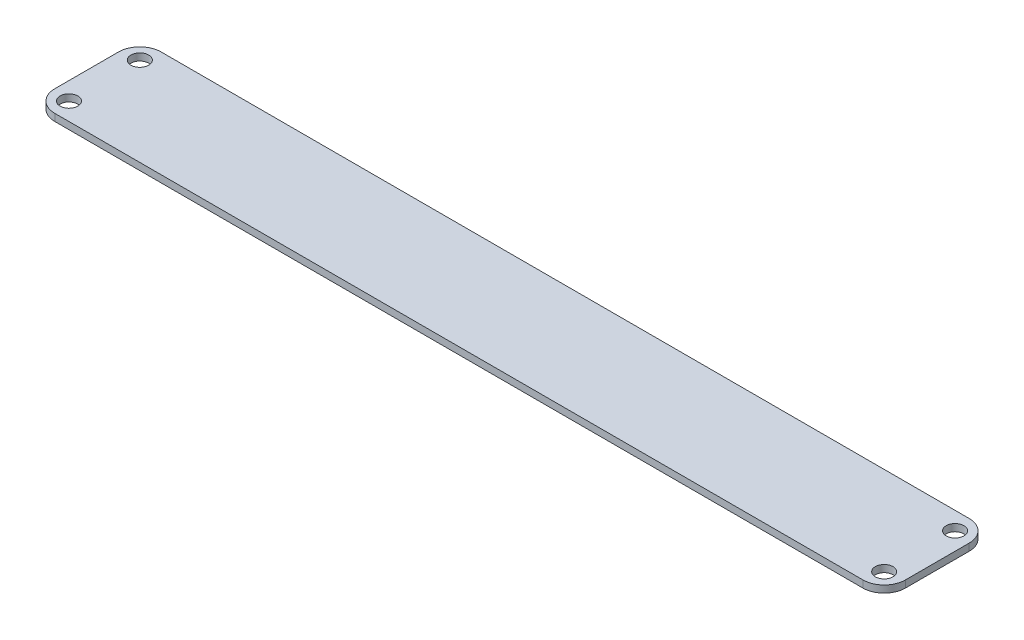
SolidWorks part; units mm, degrees
ref_plane "Front Plane" through (0, 0, 0) normal (0, 0, 1) x (1, 0, 0)
ref_plane "Top Plane" through (0, 0, 0) normal (0, 1, 0) x (1, 0, 0)
ref_plane "Right Plane" through (0, 0, 0) normal (1, 0, 0) x (0, 0, -1)
sketch "Sketch1" plane through (0, 0, 0) normal (0, 1, 0) x (1, 0, 0)
  line L1 (-60, 7.5) -> (60, 7.5)
  line L2 (-60, 7.5) -> (-60, -7.5)
  line L3 (-60, -7.5) -> (60, -7.5)
  line L4 (60, 7.5) -> (60, -7.5)
  line L5 (-60, 7.5) -> (60, -7.5) construction
  line L6 (-60, -7.5) -> (60, 7.5) construction
  point P0 (0, 0)
  dimension "D1" = 15
  dimension "D2" = 120
extrude "Boss-Extrude1" add sketch "Sketch1" along normal blind 1
fillet "Fillet1" radius 3 4 edges at (-60, 0.5, -7.5) (-60, 0.5, 7.5) (60, 0.5, -7.5) (60, 0.5, 7.5)
sketch "Sketch3" plane through (0, 1, 0) normal (0, 1, 0) x (1, 0, 0)
  line L1 (57, 7.5) -> (-57, 7.5) construction
  line L2 (-60, 4.5) -> (-60, -4.5) construction
  circle A0 centre (-57.5, 5) radius 1.25
  dimension "D1" = 2.5
  dimension "D2" = 2.5
  dimension "D3" = 2.5
extrude "Cut-Extrude1" cut sketch "Sketch3" against normal up to next (1 mm away)
mirror "Mirror1" about plane through (0, 0, 0) normal (0, 0, 1) of "Cut-Extrude1"
mirror "Mirror2" about plane through (0, 0, 0) normal (1, 0, 0) of "Mirror1", "Cut-Extrude1"
